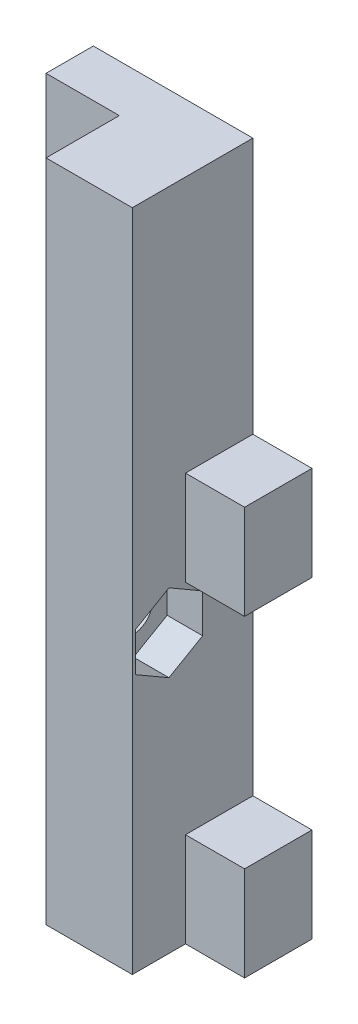
SolidWorks part; units mm, degrees
ref_plane "Alzado" through (0, 0, 0) normal (0, 0, 1) x (1, 0, 0)
ref_plane "Planta" through (0, 0, 0) normal (0, 1, 0) x (1, 0, 0)
ref_plane "Vista lateral" through (0, 0, 0) normal (1, 0, 0) x (0, 0, -1)
sketch "Croquis5" plane through (0, 0, 0) normal (0, 0, 1) x (1, 0, 0)
  line L0 (18.5, 26.5) -> (18.5, 34.5)
  line L1 (0, 0) -> (18.5, 0)
  line L2 (0, 0) -> (0, 34.5)
  line L3 (0, 34.5) -> (18.5, 34.5)
  line L4 (18.5, 0) -> (18.5, 8)
  line L5 (18.5, 26.5) -> (13.5, 26.5)
  line L7 (18.5, 8) -> (13.5, 8)
  line L8 (13.5, 26.5) -> (13.5, 8)
  dimension "D1" = 18.5
  dimension "D2" = 34.5
  dimension "D3" = 8
  dimension "D4" = 8
  dimension "D5" = 5
extrude "Saliente-Extruir3" add sketch "Croquis5" along normal blind 4
sketch "Croquis6" plane through (0, 0, 4) normal (0, 0, 1) x (1, 0, 0)
  line L1 (6.2, 34.5) -> (6.2, 0)
  line L2 (0, 34.5) -> (0, 0) construction
  line L10 (0, 34.5) -> (0, 0)
  line L11 (0, 0) -> (18.5, 0)
  line L12 (18.5, 0) -> (18.5, 8)
  line L13 (18.5, 8) -> (13.5, 8)
  line L14 (13.5, 8) -> (13.5, 26.5)
  line L15 (13.5, 26.5) -> (18.5, 26.5)
  line L16 (18.5, 26.5) -> (18.5, 34.5)
  line L17 (18.5, 34.5) -> (0, 34.5)
  line L19 (6.2, 0) -> (18.5, 0)
  line L20 (18.5, 0) -> (18.5, 8)
  line L21 (18.5, 8) -> (13.5, 8)
  line L22 (13.5, 8) -> (13.5, 26.5)
  line L23 (13.5, 26.5) -> (18.5, 26.5)
  line L24 (18.5, 26.5) -> (18.5, 34.5)
  line L25 (18.5, 34.5) -> (6.2, 34.5)
  dimension "D1" = 0
  dimension "D2" = 6.2
extrude "Saliente-Extruir4" add sketch "Croquis6" along normal blind 1.7
sketch "Croquis7" plane through (0, 0, 5.7) normal (0, 0, 1) x (1, 0, 0)
  line L0 (18.5, 34.5) -> (6.2, 34.5) construction
  line L1 (6.2, 0) -> (13.5, 0)
  line L2 (6.2, 0) -> (6.2, 34.5)
  line L3 (6.2, 34.5) -> (13.5, 34.5)
  line L4 (13.5, 0) -> (13.5, 34.5)
  line L5 (13.5, 8) -> (13.5, 26.5) construction
extrude "Saliente-Extruir5" add sketch "Croquis7" along normal blind 4.5
sketch "Croquis8" plane through (13.5, 0, 0) normal (1, 0, 0) x (0, 0, -1)
  line L0 (-4, 26.5) -> (-4, 8) construction
  line L1 (-4, 23.5) -> (-10.2, 23.5) construction
  line L2 (-10.2, 0) -> (-10.2, 34.5) construction
  line L3 (-5.7, 8) -> (0, 8) construction
  line L4 (-5.7, 26.5) -> (0, 26.5) construction
  line L5 (-10.2, 34.5) -> (-5.7, 34.5) construction
  circle A0 centre (-7.1, 23.5) radius 1.6
  dimension "D1" = 3.2
  dimension "D2" = 6.2
  dimension "D3" = 11
extrude "Cortar-Extruir3" cut sketch "Croquis8" against normal up to next
sketch "Croquis9" plane through (13.5, 0, 0) normal (1, 0, 0) x (0, 0, -1)
  line L1 (-7.1, 26.7909) -> (-9.95, 25.1454)
  line L2 (-9.95, 25.1454) -> (-9.95, 21.8546)
  line L3 (-9.95, 21.8546) -> (-7.1, 20.2091)
  line L4 (-7.1, 20.2091) -> (-4.25, 21.8546)
  line L5 (-4.25, 21.8546) -> (-4.25, 25.1454)
  line L6 (-4.25, 25.1454) -> (-7.1, 26.7909)
  circle A0 centre (-7.1, 23.5) radius 2.85 construction
  dimension "D1" = 5.7
extrude "Cortar-Extruir4" cut sketch "Croquis9" against normal blind 3
sketch "Croquis10" plane through (0, 34.5, 0) normal (0, 1, 0) x (1, 0, 0)
  line L0 (13.5, -5.7) -> (13.5, 0)
  line L8 (18.5, 0) -> (0, 0)
  line L9 (0, 0) -> (0, -4)
  line L10 (0, -4) -> (6.2, -4)
  line L11 (6.2, -4) -> (6.2, -10.2)
  line L12 (6.2, -10.2) -> (13.5, -10.2)
  line L13 (13.5, -10.2) -> (13.5, -5.7)
  line L14 (13.5, -5.7) -> (18.5, -5.7)
  line L15 (18.5, -5.7) -> (18.5, 0)
  line L16 (13.5, 0) -> (0, 0)
  line L17 (0, 0) -> (0, -4)
  line L18 (0, -4) -> (6.2, -4)
  line L19 (6.2, -4) -> (6.2, -10.2)
  line L20 (6.2, -10.2) -> (13.5, -10.2)
  line L21 (13.5, -10.2) -> (13.5, -5.7)
  dimension "D1" = 0
extrude "Saliente-Extruir6" add sketch "Croquis10" along normal blind 21.7
